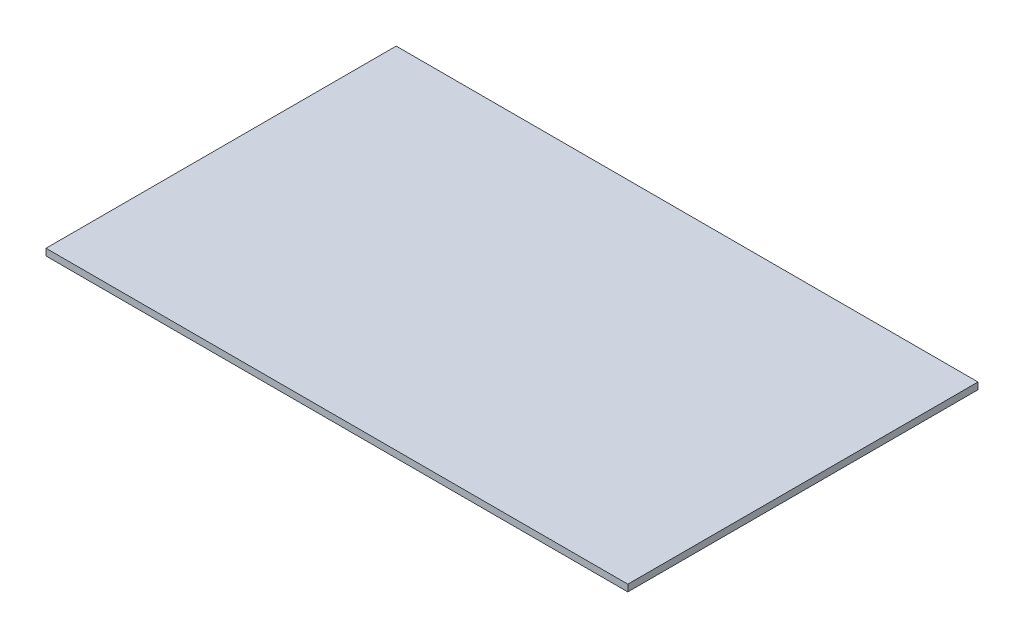
SolidWorks part; units mm, degrees
ref_plane "Front Plane" through (0, 0, 0) normal (0, 0, 1) x (1, 0, 0)
ref_plane "Top Plane" through (0, 0, 0) normal (0, 1, 0) x (1, 0, 0)
ref_plane "Right Plane" through (0, 0, 0) normal (1, 0, 0) x (0, 0, -1)
sketch "Sketch1" plane through (0, 0, 0) normal (0, 1, 0) x (1, 0, 0)
  line L1 (-30.1173, 7.9488) -> (56.2827, 7.9488)
  line L2 (-30.1173, 7.9488) -> (-30.1173, -44.0512)
  line L3 (-30.1173, -44.0512) -> (56.2827, -44.0512)
  line L4 (56.2827, 7.9488) -> (56.2827, -44.0512)
  dimension "D1" = 86.4
  dimension "D2" = 52
extrude "Boss-Extrude1" add sketch "Sketch1" along normal blind 1
